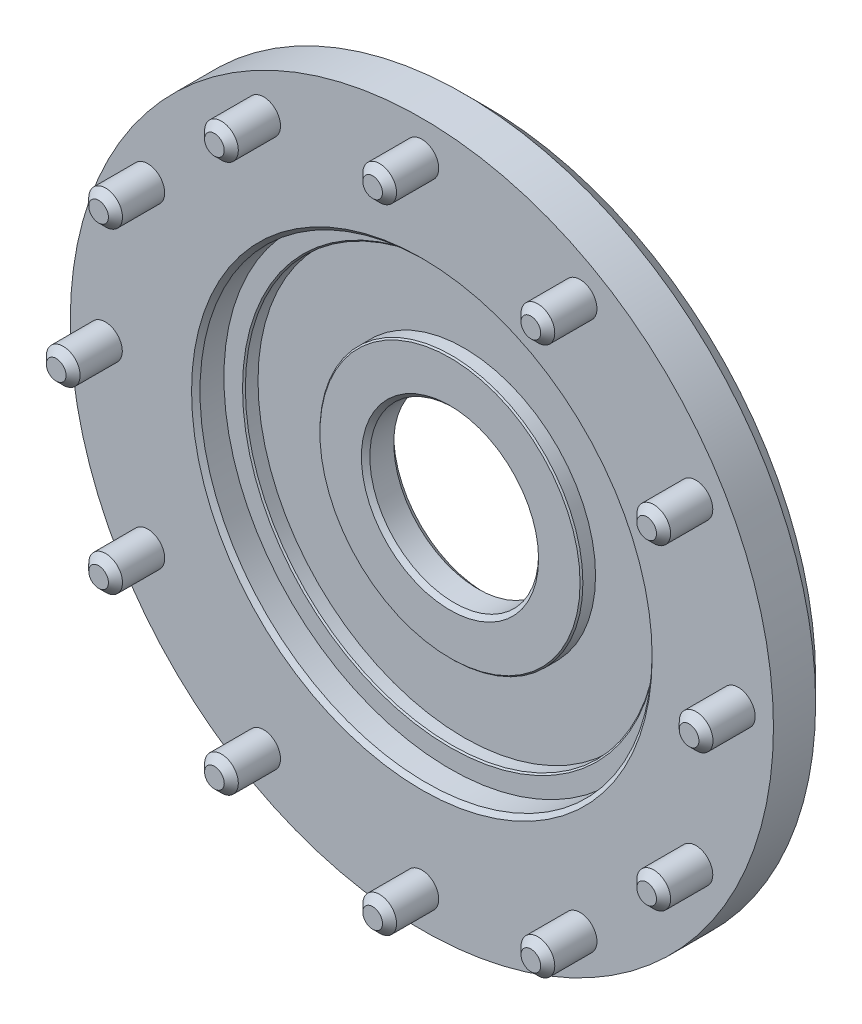
SolidWorks part; units mm, degrees
ref_plane "Front Plane" through (0, 0, 0) normal (0, 0, 1) x (1, 0, 0)
ref_plane "Top Plane" through (0, 0, 0) normal (0, 1, 0) x (1, 0, 0)
ref_plane "Right Plane" through (0, 0, 0) normal (1, 0, 0) x (0, 0, -1)
sketch "Sketch1" plane through (0, 0, 0) normal (0, 0, 1) x (1, 0, 0)
  circle A0 centre (0, 0) radius 50
  dimension "D1" = 100
extrude "Boss-Extrude1" add sketch "Sketch1" against normal blind 9
sketch "Sketch2" plane through (0, 0, 0) normal (0, 0, 1) x (1, 0, 0)
  circle A0 centre (0, 0) radius 45 construction
  circle A1 centre (45, 0) radius 2.4
  dimension "D1" = 90
  dimension "D2" = 4.8
extrude "Boss-Extrude2" add sketch "Sketch2" along normal blind 7
chamfer "Chamfer1" distance 1 angle 45 1 edges at (47.4, 0, 7)
pattern_circular "CirPattern1" count 12 over 360 about axis through (0, 0, 0) along (0, 0, 1) of "Boss-Extrude2", "Chamfer1"
sketch "Sketch3" plane through (0, 0, 0) normal (0, 0, 1) x (1, 0, 0)
  circle A0 centre (0, 0) radius 32.15
  dimension "D1" = 64.3
extrude "Cut-Extrude1" cut sketch "Sketch3" against normal blind 4
sketch "Sketch4" plane through (0, 0, 0) normal (0, 0, 1) x (1, 0, 0)
  circle A0 centre (0, 0) radius 12
  dimension "D1" = 24
extrude "Cut-Extrude2" cut sketch "Sketch4" against normal through all
chamfer "Chamfer2" distance 0.6 angle 45 1 edges at (32.15, 0, 0)
sketch "Sketch5" plane through (0, 0, -4) normal (0, 0, 1) x (1, 0, 0)
  line L0 (-29.3, 0) -> (-18.7, 0) construction
  circle A0 centre (0, 0) radius 24 construction
  circle A1 centre (0, 0) radius 18.7
  circle A2 centre (0, 0) radius 29.3
  point P4 (-24, 0)
  point P8 (-24, 0)
  dimension "D1" = 48
  dimension "D2" = 10.6
extrude "Cut-Extrude3" cut sketch "Sketch5" against normal blind 2
chamfer "Chamfer3" distance 0.2 angle 45 2 edges at (18.7, 0, -4) (29.3, 0, -4)
chamfer "Chamfer4" distance 3 angle 45 1 edges at (50, 0, -9)
chamfer "Chamfer5" distance 1 angle 45 1 edges at (12, 0, -9)
chamfer "Chamfer6" distance 0.6 angle 45 1 edges at (12, 0, -4)
